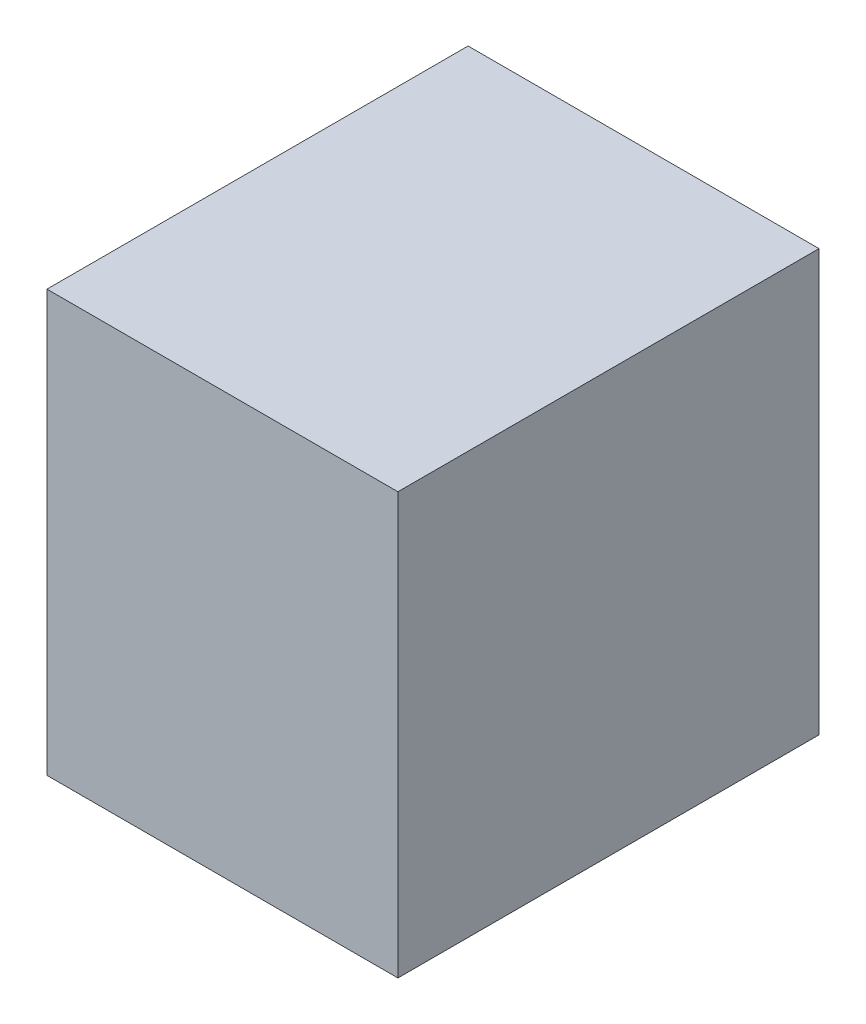
SolidWorks part; units mm, degrees
ref_plane "Front Plane" through (0, 0, 0) normal (0, 0, 1) x (1, 0, 0)
ref_plane "Top Plane" through (0, 0, 0) normal (0, 1, 0) x (1, 0, 0)
ref_plane "Right Plane" through (0, 0, 0) normal (1, 0, 0) x (0, 0, -1)
sketch "Sketch1" plane through (0, 0, 0) normal (0, 1, 0) x (1, 0, 0)
  line L1 (254, -304.8) -> (-254, -304.8)
  line L2 (254, -304.8) -> (254, 304.8)
  line L3 (254, 304.8) -> (-254, 304.8)
  line L4 (-254, -304.8) -> (-254, 304.8)
  line L5 (254, -304.8) -> (-254, 304.8) construction
  line L6 (254, 304.8) -> (-254, -304.8) construction
  point P0 (0, 0)
  dimension "D1" = 609.6
  dimension "D2" = 508
extrude "Boss-Extrude1" add sketch "Sketch1" along normal blind 609.6
